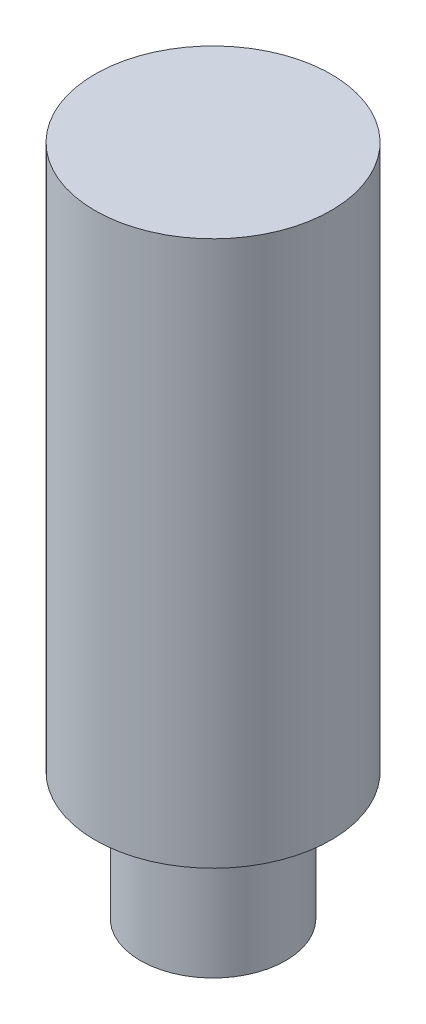
SolidWorks part; units mm, degrees
ref_plane "Front Plane" through (0, 0, 0) normal (0, 0, 1) x (1, 0, 0)
ref_plane "Top Plane" through (0, 0, 0) normal (0, 1, 0) x (1, 0, 0)
ref_plane "Right Plane" through (0, 0, 0) normal (1, 0, 0) x (0, 0, -1)
sketch "Sketch1" plane through (0, 0, 0) normal (0, 1, 0) x (1, 0, 0)
  circle A0 centre (0, 0) radius 4
  dimension "D1" = 8
extrude "Boss-Extrude1" add sketch "Sketch1" along normal mid plane 7
sketch "Sketch2" plane through (0, 3.5, 0) normal (0, 1, 0) x (1, 0, 0)
  circle A0 centre (0, 0) radius 6.5
  dimension "D1" = 13
extrude "Boss-Extrude2" add sketch "Sketch2" along normal blind 30
